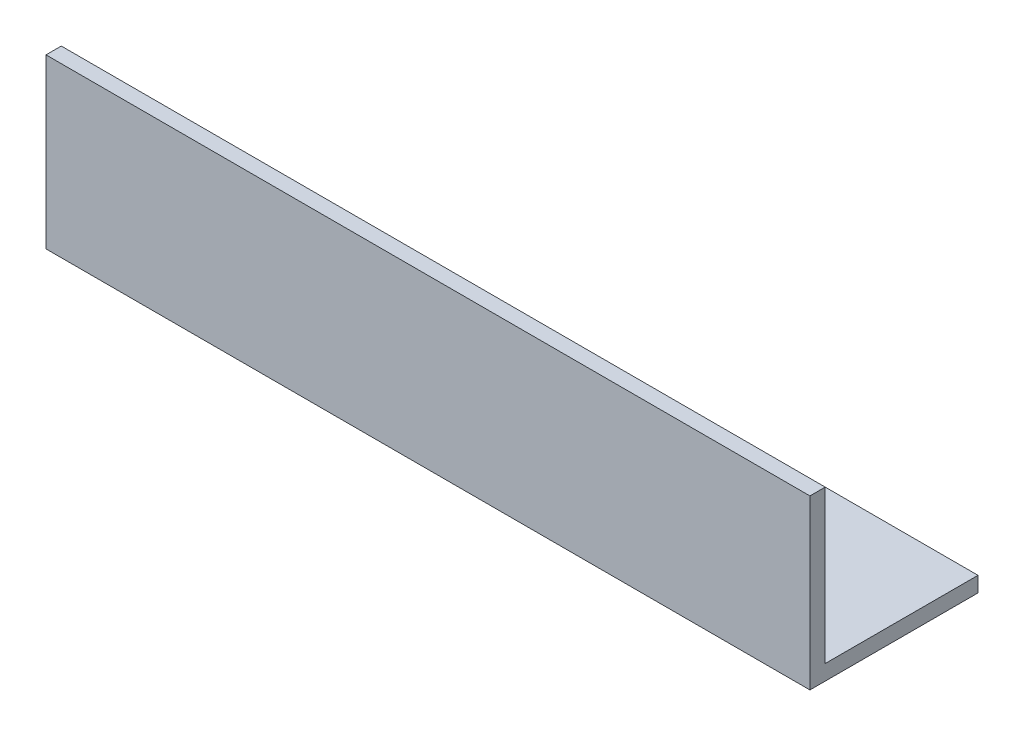
SolidWorks part; units mm, degrees
ref_plane "Спереди" through (0, 0, 0) normal (0, 0, 1) x (1, 0, 0)
ref_plane "Сверху" through (0, 0, 0) normal (0, 1, 0) x (1, 0, 0)
ref_plane "Справа" through (0, 0, 0) normal (1, 0, 0) x (0, 0, -1)
sketch "Эскиз1" plane through (0, 0, 0) normal (1, 0, 0) x (0, 0, -1)
  line L0 (0, 30) -> (0, 0)
  line L1 (0, 0) -> (30, 0)
extrude "Вытянуть-Тонкостенный1" add sketch "Эскиз1" along normal blind 150 thin
